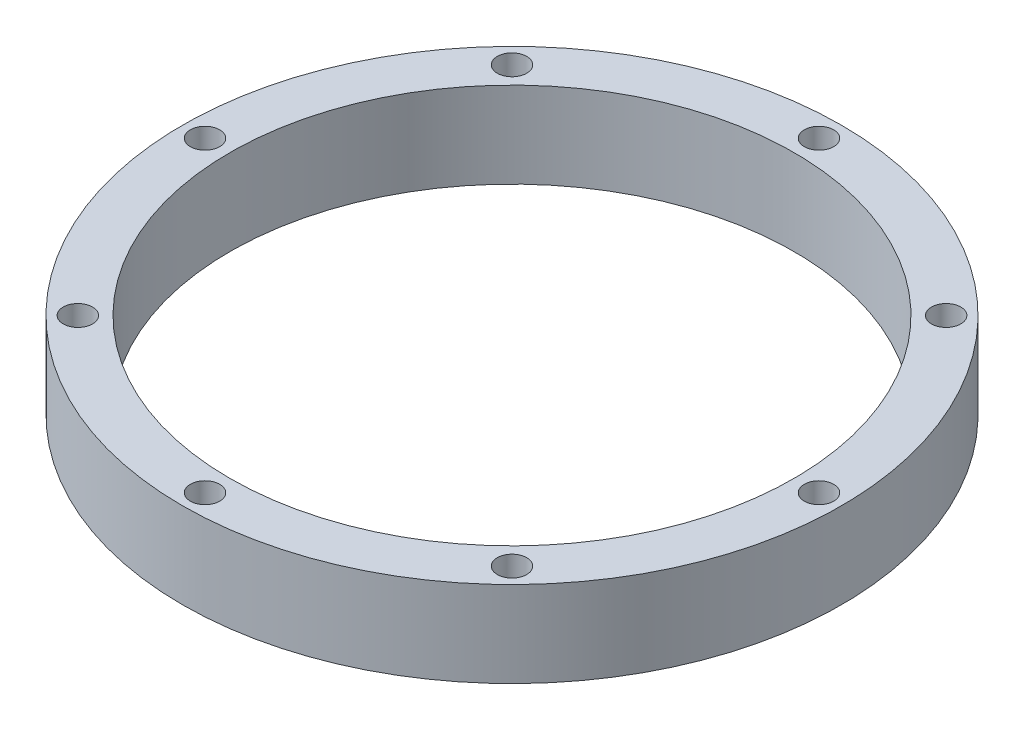
SolidWorks part; units mm, degrees
material "AISI 1045 Steel, cold drawn"
ref_plane "Front Plane" through (0, 0, 0) normal (0, 0, 1) x (1, 0, 0)
ref_plane "Top Plane" through (0, 0, 0) normal (0, 1, 0) x (1, 0, 0)
ref_plane "Right Plane" through (0, 0, 0) normal (1, 0, 0) x (0, 0, -1)
sketch "Sketch1" plane through (0, 0, 0) normal (0, 1, 0) x (1, 0, 0)
  circle A0 centre (0, 0) radius 73
  circle A1 centre (0, 0) radius 62.5
  circle A2 centre (-48.0833, 48.0833) radius 3.25
  circle A3 centre (-68, 0) radius 3.25
  circle A4 centre (0, 68) radius 3.25
  circle A5 centre (48.0833, 48.0833) radius 3.25
  circle A6 centre (68, 0) radius 3.25
  circle A7 centre (48.0833, -48.0833) radius 3.25
  circle A8 centre (0, -68) radius 3.25
  circle A9 centre (-48.0833, -48.0833) radius 3.25
  point P22 (0, 0)
  point P24 (0, 0)
  dimension "D1" = 146
  dimension "D2" = 125
  dimension "D3" = 68
  dimension "D4" = 6.5
  dimension "D5" = 8
extrude "Boss-Extrude1" add sketch "Sketch1" along normal blind 19
